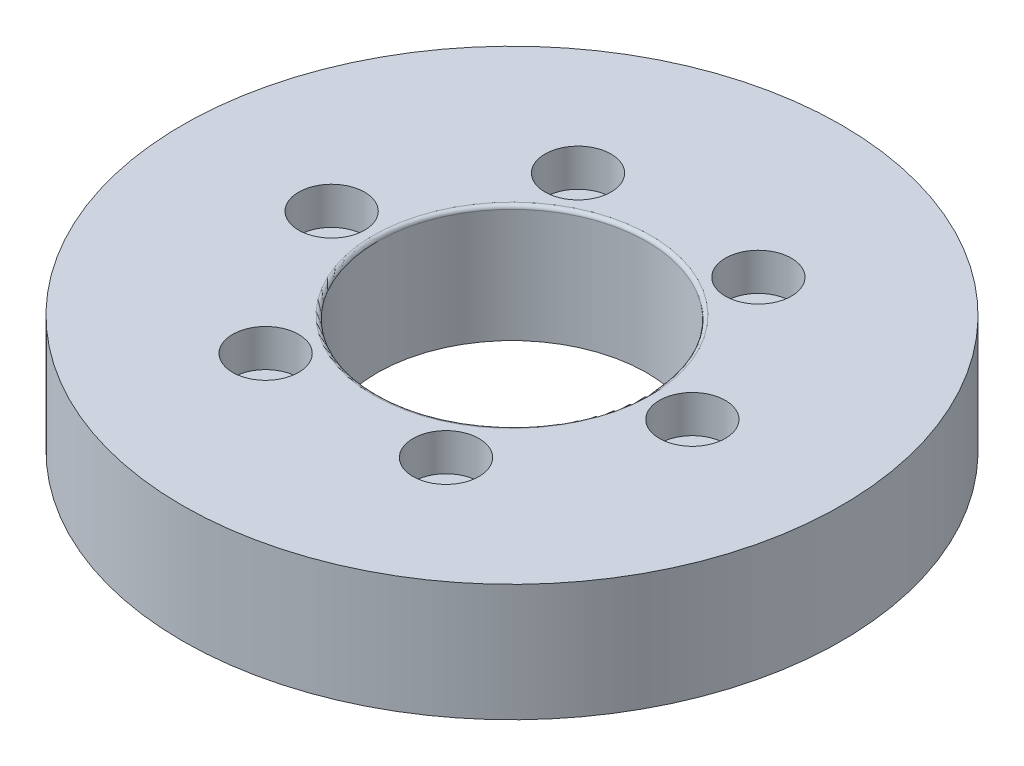
SolidWorks part; units mm, degrees
ref_plane "前视基准面" through (0, 0, 0) normal (0, 0, 1) x (1, 0, 0)
ref_plane "上视基准面" through (0, 0, 0) normal (0, 1, 0) x (1, 0, 0)
ref_plane "右视基准面" through (0, 0, 0) normal (1, 0, 0) x (0, 0, -1)
sketch "草图1" plane through (0, 0, 0) normal (0, 1, 0) x (1, 0, 0)
  circle A0 centre (0, 0) radius 44.95
  circle A1 centre (0, 0) radius 24.6 construction
  circle A2 centre (-24.6, 0) radius 2.5
  circle A3 centre (-12.3, 21.3042) radius 2.5
  circle A4 centre (12.3, 21.3042) radius 2.5
  circle A5 centre (24.6, 0) radius 2.5
  circle A6 centre (12.3, -21.3042) radius 2.5
  circle A7 centre (-12.3, -21.3042) radius 2.5
  circle A8 centre (0, 0) radius 18.4
  point P19 (0, 0)
  dimension "D1" = 6
  dimension "D2" = 89.9
extrude "凸台-拉伸1" add sketch "草图1" along normal blind 16
sketch "草图2" plane through (0, 0, 0) normal (0, -1, 0) x (1, 0, 0)
  circle A0 centre (0, 0) radius 24.6 construction
  circle A1 centre (-21.3042, -12.3) radius 4
  circle A2 centre (0, 24.6) radius 4
  circle A3 centre (21.3042, -12.3) radius 4
  point P17 (0, 0)
  dimension "D1" = 3
extrude "切除-拉伸1" cut sketch "草图2" against normal blind 3
sketch "草图4" plane through (0, 16, 0) normal (0, 1, 0) x (1, 0, 0)
  circle A0 centre (-24.6, 0) radius 4.5
  circle A1 centre (0, 0) radius 24.6 construction
  circle A2 centre (-12.3, 21.3042) radius 4.5
  circle A3 centre (12.3, 21.3042) radius 4.5
  circle A4 centre (24.6, 0) radius 4.5
  circle A5 centre (12.3, -21.3042) radius 4.5
  circle A6 centre (-12.3, -21.3042) radius 4.5
  point P16 (0, 0)
  dimension "D1" = 6
extrude "切除-拉伸2" cut sketch "草图4" against normal blind 5.1
ref_plane "基准面1" through (43, 0, 0) normal (1, 0, 0) x (0, 0, -1)
sketch "草图5" plane through (43, 0, 0) normal (1, 0, 0) x (0, 0, -1)
  circle A0 centre (0, 12) radius 1.5
extrude "切除-拉伸3" cut sketch "草图5" against normal blind 10
pattern_circular "阵列(圆周)1" count 12 every 30 about axis through (0, 0, 0) along (0, 1, 0) of "切除-拉伸3"
fillet "圆角1" radius 0.5 1 edges at (0, 16, 18.4)
